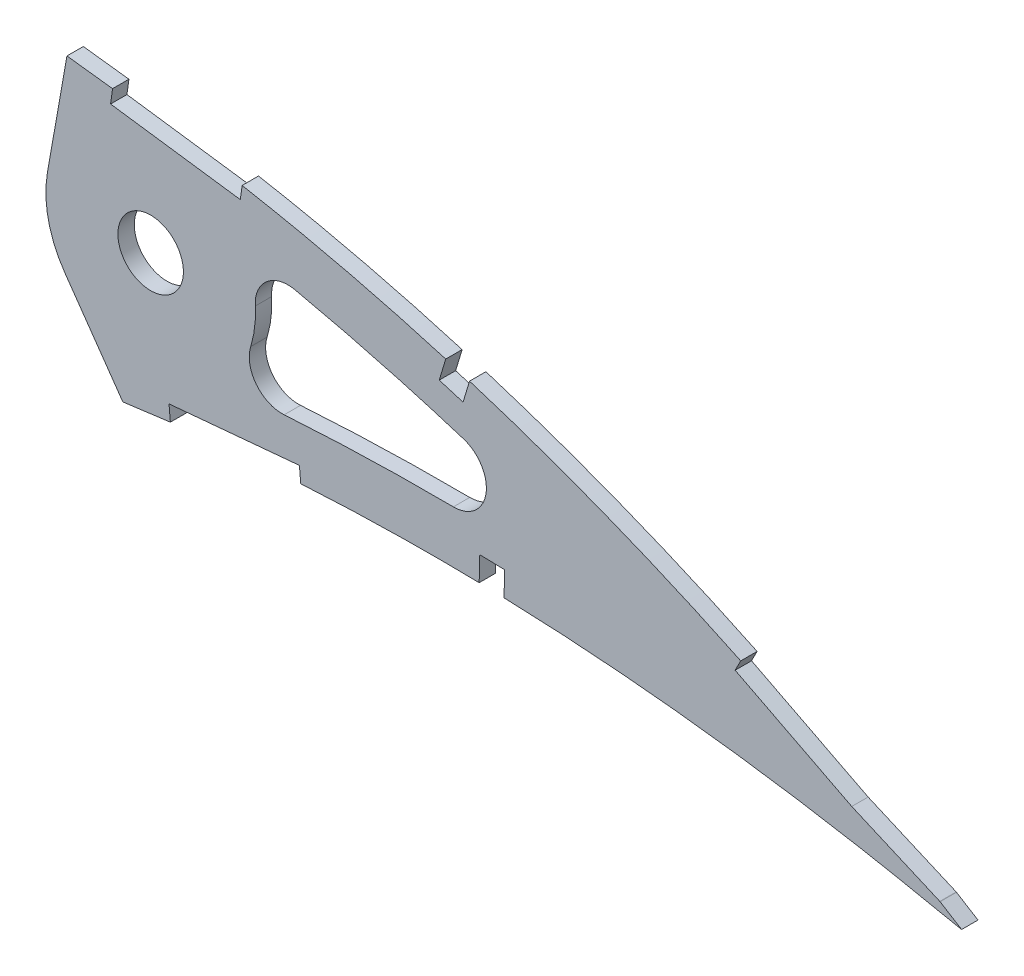
SolidWorks part; units mm, degrees
material "Pine"
ref_plane "Front Plane" through (0, 0, 0) normal (0, 0, 1) x (1, 0, 0)
ref_plane "Top Plane" through (0, 0, 0) normal (0, 1, 0) x (1, 0, 0)
ref_plane "Right Plane" through (0, 0, 0) normal (1, 0, 0) x (0, 0, -1)
curve "Curve2"
  spline degree 3 poles (520.229, 0.8111, 0) (520.1892, 0.8357, 0) (520.0299, 0.9341, 0) (519.6711, 1.1542, 0) (519.0735, 1.5208, 0) (518.237, 2.0313, 0) (517.1622, 2.6844, 0) (515.8486, 3.4756, 0) (514.2969, 4.4021, 0) (512.5075, 5.4598, 0) (510.4807, 6.6436, 0) (508.2172, 7.9486, 0) (505.7172, 9.3676, 0) (502.9816, 10.8948, 0) (500.0114, 12.5227, 0) (496.8072, 14.2443, 0) (493.3701, 16.0505, 0) (489.7015, 17.9338, 0) (485.8019, 19.8836, 0) (481.6733, 21.8919, 0) (477.317, 23.9487, 0) (472.7345, 26.0429, 0) (467.9284, 28.1661, 0) (462.9001, 30.305, 0) (457.6524, 32.4505, 0) (452.1876, 34.5902, 0) (446.5089, 36.7144, 0) (440.6184, 38.8094, 0) (434.5207, 40.866, 0) (428.2186, 42.8708, 0) (421.7166, 44.813, 0) (415.0186, 46.68, 0) (408.1302, 48.4622, 0) (401.0555, 50.1466, 0) (393.8008, 51.7219, 0) (386.3718, 53.1787, 0) (378.7746, 54.5024, 0) (371.0303, 55.692, 0) (363.2636, 56.6815, 0) (355.5128, 57.652, 0) (347.7736, 58.5637, 0) (339.9398, 59.4368, 0) (332.019, 60.2663, 0) (324.019, 61.0497, 0) (315.9478, 61.7836, 0) (307.814, 62.4658, 0) (299.6253, 63.0925, 0) (291.3904, 63.6628, 0) (283.1174, 64.1714, 0) (274.8152, 64.6183, 0) (266.4922, 65.0001, 0) (258.157, 65.3142, 0) (249.8185, 65.5589, 0) (241.4854, 65.7316, 0) (233.1666, 65.8314, 0) (224.8708, 65.8555, 0) (216.6071, 65.8035, 0) (208.384, 65.6736, 0) (200.2107, 65.464, 0) (192.0958, 65.1743, 0) (184.048, 64.8046, 0) (176.0762, 64.3519, 0) (168.189, 63.8191, 0) (160.3952, 63.2038, 0) (152.7034, 62.506, 0) (145.1216, 61.7286, 0) (137.6583, 60.8693, 0) (130.3214, 59.9308, 0) (123.1191, 58.9147, 0) (116.0593, 57.8206, 0) (109.1496, 56.6517, 0) (102.3976, 55.409, 0) (95.8102, 54.0963, 0) (89.3948, 52.714, 0) (83.1581, 51.266, 0) (77.1065, 49.7551, 0) (71.2467, 48.1838, 0) (65.5845, 46.5561, 0) (60.1256, 44.8756, 0) (54.8764, 43.1442, 0) (49.8409, 41.3683, 0) (45.0253, 39.5493, 0) (40.4333, 37.6928, 0) (36.0702, 35.8014, 0) (31.9393, 33.8806, 0) (28.0452, 31.9329, 0) (24.3908, 29.9636, 0) (20.9797, 27.9757, 0) (17.8153, 25.973, 0) (14.8987, 23.9604, 0) (12.2341, 21.9394, 0) (9.8224, 19.9149, 0) (7.6651, 17.8901, 0) (5.7652, 15.8664, 0) (4.1228, 13.8473, 0) (2.7399, 11.8344, 0) (1.6168, 9.8297, 0) (0.7561, 7.8345, 0) (0.1568, 5.85, 0) (-0.1712, 3.8792, 0) (-0.2528, 1.9205, 0) (-0.0842, 0.6392, 0) (0, 0, 0) knots 0 0 0 0 0.000254 0.001015 0.002283 0.004057 0.006331 0.009105 0.012374 0.016134 0.02038 0.025106 0.030306 0.035972 0.0421 0.048678 0.055702 0.06316 0.071046 0.07935 0.088063 0.097176 0.106678 0.116562 0.126814 0.137428 0.148394 0.1597 0.171338 0.183298 0.19557 0.208144 0.221012 0.234162 0.247587 0.261277 0.275223 0.289414 0.303771 0.317689 0.331784 0.34604 0.360444 0.374983 0.38964 0.404403 0.419257 0.434187 0.449177 0.464215 0.479284 0.49437 0.509458 0.524532 0.539579 0.554583 0.56953 0.584403 0.599191 0.613877 0.628447 0.642889 0.657186 0.671326 0.685294 0.699078 0.712665 0.726043 0.739198 0.752118 0.764792 0.777208 0.789356 0.801224 0.812804 0.824083 0.835055 0.84571 0.856038 0.866034 0.875689 0.884998 0.893953 0.902553 0.910789 0.918661 0.926166 0.933303 0.940071 0.946475 0.952518 0.958205 0.963547 0.968557 0.97325 0.977651 0.981787 0.985694 0.989415 0.993001 0.996508 1 1 1 1
curve "Curve3"
  spline degree 3 poles (0, 0, 0) (0.1336, -0.6306, 0) (0.4014, -1.8948, 0) (1.129, -3.7148, 0) (2.0912, -5.4642, 0) (3.3081, -7.1386, 0) (4.7718, -8.7374, 0) (6.479, -10.2623, 0) (8.428, -11.7125, 0) (10.6162, -13.0874, 0) (13.0406, -14.3883, 0) (15.6982, -15.6145, 0) (18.5868, -16.7656, 0) (21.7032, -17.8401, 0) (25.0435, -18.8396, 0) (28.6046, -19.7616, 0) (32.3825, -20.6074, 0) (36.3735, -21.375, 0) (40.5732, -22.065, 0) (44.9774, -22.6771, 0) (49.5814, -23.2117, 0) (54.3808, -23.6676, 0) (59.3708, -24.0458, 0) (64.5464, -24.3466, 0) (69.9027, -24.5709, 0) (75.4344, -24.718, 0) (81.1363, -24.7899, 0) (87.003, -24.788, 0) (93.0289, -24.7115, 0) (99.2088, -24.5648, 0) (105.5368, -24.3469, 0) (112.0073, -24.0604, 0) (118.6142, -23.7083, 0) (125.3518, -23.2917, 0) (132.2141, -22.8125, 0) (139.1951, -22.2745, 0) (146.2885, -21.679, 0) (153.4882, -21.0296, 0) (160.7876, -20.3295, 0) (168.1806, -19.5808, 0) (175.6606, -18.7872, 0) (183.2209, -17.9512, 0) (190.8551, -17.0772, 0) (198.5563, -16.1668, 0) (206.3179, -15.2253, 0) (214.1326, -14.2544, 0) (221.9939, -13.2579, 0) (229.8947, -12.2404, 0) (237.8276, -11.2019, 0) (245.786, -10.1497, 0) (253.7621, -9.0829, 0) (261.7491, -8.0072, 0) (269.7395, -6.9257, 0) (277.7256, -5.8389, 0) (285.7003, -4.7513, 0) (293.6562, -3.6657, 0) (301.5856, -2.5824, 0) (309.4812, -1.5067, 0) (317.3352, -0.4385, 0) (325.1402, 0.6201, 0) (332.8888, 1.6659, 0) (340.5737, 2.6975, 0) (348.187, 3.7144, 0) (355.721, 4.7168, 0) (363.0553, 5.6745, 0) (370.1707, 6.6383, 0) (377.0913, 7.4284, 0) (383.9258, 8.1028, 0) (390.6811, 8.6557, 0) (397.3493, 9.0951, 0) (403.9227, 9.4241, 0) (410.3934, 9.6473, 0) (416.7532, 9.7713, 0) (422.9943, 9.7993, 0) (429.1081, 9.7402, 0) (435.0867, 9.5987, 0) (440.9216, 9.3813, 0) (446.6049, 9.0952, 0) (452.1283, 8.7483, 0) (457.4837, 8.3456, 0) (462.6634, 7.8966, 0) (467.6597, 7.4078, 0) (472.4647, 6.8849, 0) (477.0715, 6.3387, 0) (481.4727, 5.7729, 0) (485.6616, 5.1968, 0) (489.6316, 4.6162, 0) (493.3764, 4.0385, 0) (496.89, 3.4693, 0) (500.1667, 2.916, 0) (503.2016, 2.384, 0) (505.9892, 1.8782, 0) (508.5257, 1.4052, 0) (510.8062, 0.9673, 0) (512.8275, 0.5717, 0) (514.5859, 0.2202, 0) (516.0789, -0.0824, 0) (517.3037, -0.3347, 0) (518.2586, -0.5328, 0) (518.9417, -0.6767, 0) (519.3522, -0.7624, 0) (519.5346, -0.8013, 0) (519.5802, -0.8111, 0) knots 0 0 0 0 0.003638 0.007293 0.011028 0.014901 0.018963 0.023258 0.027821 0.032679 0.037853 0.043362 0.049215 0.055422 0.061989 0.068918 0.076211 0.083868 0.091887 0.100266 0.109 0.118085 0.127515 0.137285 0.147388 0.157816 0.168563 0.179619 0.190977 0.202627 0.21456 0.226767 0.239236 0.251959 0.264924 0.27812 0.291536 0.30516 0.318981 0.332985 0.347163 0.361499 0.375981 0.390597 0.405333 0.420175 0.43511 0.450124 0.465203 0.480333 0.495501 0.51069 0.525887 0.541078 0.556247 0.571382 0.586466 0.601485 0.616424 0.631269 0.646007 0.660621 0.675098 0.689423 0.703582 0.716908 0.730009 0.742952 0.755726 0.76832 0.780724 0.792927 0.804916 0.816679 0.828204 0.839475 0.850481 0.861208 0.871639 0.881763 0.891564 0.901027 0.910139 0.918884 0.927249 0.935221 0.942785 0.949928 0.956638 0.962904 0.968712 0.974054 0.978918 0.983297 0.98718 0.990561 0.993433 0.995791 0.99763 0.998946 0.999737 1 1 1 1
sketch "Sketch1" plane through (0, 0, 0) normal (0, 0, 1) x (1, 0, 0)
  line L1 (519.5802, -0.8111) -> (524.4049, -1.7687)
  line L2 (520.229, 0.8111) -> (524.4049, -1.7687)
  spline S0 degree 3 poles (-2903.7635, -749.124) (66.2436, 68.8235) (-8.6937, 20.855) (1.129, -3.7148) (2.0912, -5.4642) (3.3081, -7.1386) (4.7718, -8.7374) (6.479, -10.2623) (8.428, -11.7125) (10.6162, -13.0874) (13.0406, -14.3883) (15.6982, -15.6145) (18.5868, -16.7656) (21.7032, -17.8401) (25.0435, -18.8396) (28.6046, -19.7616) (32.3825, -20.6074) (36.3735, -21.375) (40.5732, -22.065) (44.9774, -22.6771) (49.5814, -23.2117) (54.3808, -23.6676) (59.3708, -24.0458) (64.5464, -24.3466) (69.9027, -24.5709) (75.4344, -24.718) (81.1363, -24.7899) (87.003, -24.788) (93.0289, -24.7115) (99.2088, -24.5648) (105.5368, -24.3469) (112.0073, -24.0604) (118.6142, -23.7083) (125.3518, -23.2917) (132.2141, -22.8125) (139.1951, -22.2745) (146.2885, -21.679) (153.4882, -21.0296) (160.7876, -20.3295) (168.1806, -19.5808) (175.6606, -18.7872) (183.2209, -17.9512) (190.8551, -17.0772) (198.5563, -16.1668) (206.3179, -15.2253) (214.1326, -14.2544) (221.9939, -13.2579) (229.8947, -12.2404) (237.8276, -11.2019) (245.786, -10.1497) (253.7621, -9.0829) (261.7491, -8.0072) (269.7395, -6.9257) (277.7256, -5.8389) (285.7003, -4.7513) (293.6562, -3.6657) (301.5856, -2.5824) (309.4812, -1.5067) (317.3352, -0.4385) (325.1402, 0.6201) (332.8888, 1.6659) (340.5737, 2.6975) (348.187, 3.7144) (355.721, 4.7168) (363.0553, 5.6745) (370.1707, 6.6383) (377.0913, 7.4284) (383.9258, 8.1028) (390.6811, 8.6557) (397.3493, 9.0951) (403.9227, 9.4241) (410.3934, 9.6473) (416.7532, 9.7713) (422.9943, 9.7993) (429.1081, 9.7402) (435.0867, 9.5987) (440.9216, 9.3813) (446.6049, 9.0952) (452.1283, 8.7483) (457.4837, 8.3456) (462.6634, 7.8966) (467.6597, 7.4078) (472.4647, 6.8849) (477.0715, 6.3387) (481.4727, 5.7729) (485.6616, 5.1968) (489.6316, 4.6162) (493.3764, 4.0385) (496.89, 3.4693) (500.1667, 2.916) (503.2016, 2.384) (505.9892, 1.8782) (508.5257, 1.4052) (510.8062, 0.9673) (512.8275, 0.5717) (514.5859, 0.2202) (516.0789, -0.0824) (517.3037, -0.3347) (518.2586, -0.5328) (518.9417, -0.6767) (537.0698, -4.4604) (553.3394, -15.9066) (1193.1482, 2921.6684) knots -0.137857 -0.137857 -0.137857 -0.137857 0.003638 0.007293 0.011028 0.014901 0.018963 0.023258 0.027821 0.032679 0.037853 0.043362 0.049215 0.055422 0.061989 0.068918 0.076211 0.083868 0.091887 0.100266 0.109 0.118085 0.127515 0.137285 0.147388 0.157816 0.168563 0.179619 0.190977 0.202627 0.21456 0.226767 0.239236 0.251959 0.264924 0.27812 0.291536 0.30516 0.318981 0.332985 0.347163 0.361499 0.375981 0.390597 0.405333 0.420175 0.43511 0.450124 0.465203 0.480333 0.495501 0.51069 0.525887 0.541078 0.556247 0.571382 0.586466 0.601485 0.616424 0.631269 0.646007 0.660621 0.675098 0.689423 0.703582 0.716908 0.730009 0.742952 0.755726 0.76832 0.780724 0.792927 0.804916 0.816679 0.828204 0.839475 0.850481 0.861208 0.871639 0.881763 0.891564 0.901027 0.910139 0.918884 0.927249 0.935221 0.942785 0.949928 0.956638 0.962904 0.968712 0.974054 0.978918 0.983297 0.98718 0.990561 0.993433 0.995791 0.99763 0.998946 0.999737 1.102307 1.102307 1.102307 1.102307 only from (0, 0) to (519.5802, -0.8111) construction
  spline S1 degree 3 poles (2144.5607, 2521.6799) (550.9976, -26.3511) (537.2872, -9.6513) (519.6711, 1.1542) (519.0735, 1.5208) (518.237, 2.0313) (517.1622, 2.6844) (515.8486, 3.4756) (514.2969, 4.4021) (512.5075, 5.4598) (510.4807, 6.6436) (508.2172, 7.9486) (505.7172, 9.3676) (502.9816, 10.8948) (500.0114, 12.5227) (496.8072, 14.2443) (493.3701, 16.0505) (489.7015, 17.9338) (485.8019, 19.8836) (481.6733, 21.8919) (477.317, 23.9487) (472.7345, 26.0429) (467.9284, 28.1661) (462.9001, 30.305) (457.6524, 32.4505) (452.1876, 34.5902) (446.5089, 36.7144) (440.6184, 38.8094) (434.5207, 40.866) (428.2186, 42.8708) (421.7166, 44.813) (415.0186, 46.68) (408.1302, 48.4622) (401.0555, 50.1466) (393.8008, 51.7219) (386.3718, 53.1787) (378.7746, 54.5024) (371.0303, 55.692) (363.2636, 56.6815) (355.5128, 57.652) (347.7736, 58.5637) (339.9398, 59.4368) (332.019, 60.2663) (324.019, 61.0497) (315.9478, 61.7836) (307.814, 62.4658) (299.6253, 63.0925) (291.3904, 63.6628) (283.1174, 64.1714) (274.8152, 64.6183) (266.4922, 65.0001) (258.157, 65.3142) (249.8185, 65.5589) (241.4854, 65.7316) (233.1666, 65.8314) (224.8708, 65.8555) (216.6071, 65.8035) (208.384, 65.6736) (200.2107, 65.464) (192.0958, 65.1743) (184.048, 64.8046) (176.0762, 64.3519) (168.189, 63.8191) (160.3952, 63.2038) (152.7034, 62.506) (145.1216, 61.7286) (137.6583, 60.8693) (130.3214, 59.9308) (123.1191, 58.9147) (116.0593, 57.8206) (109.1496, 56.6517) (102.3976, 55.409) (95.8102, 54.0963) (89.3948, 52.714) (83.1581, 51.266) (77.1065, 49.7551) (71.2467, 48.1838) (65.5845, 46.5561) (60.1256, 44.8756) (54.8764, 43.1442) (49.8409, 41.3683) (45.0253, 39.5493) (40.4333, 37.6928) (36.0702, 35.8014) (31.9393, 33.8806) (28.0452, 31.9329) (24.3908, 29.9636) (20.9797, 27.9757) (17.8153, 25.973) (14.8987, 23.9604) (12.2341, 21.9394) (9.8224, 19.9149) (7.6651, 17.8901) (5.7652, 15.8664) (4.1228, 13.8473) (2.7399, 11.8344) (1.6168, 9.8297) (0.7561, 7.8345) (0.1568, 5.85) (-0.1712, 3.8792) (-1.2714, -22.5145) (85.5395, -42.7616) (-2987.8188, -259.5241) knots -0.109813 -0.109813 -0.109813 -0.109813 0.000254 0.001015 0.002283 0.004057 0.006331 0.009105 0.012374 0.016134 0.02038 0.025106 0.030306 0.035972 0.0421 0.048678 0.055702 0.06316 0.071046 0.07935 0.088063 0.097176 0.106678 0.116562 0.126814 0.137428 0.148394 0.1597 0.171338 0.183298 0.19557 0.208144 0.221012 0.234162 0.247587 0.261277 0.275223 0.289414 0.303771 0.317689 0.331784 0.34604 0.360444 0.374983 0.38964 0.404403 0.419257 0.434187 0.449177 0.464215 0.479284 0.49437 0.509458 0.524532 0.539579 0.554583 0.56953 0.584403 0.599191 0.613877 0.628447 0.642889 0.657186 0.671326 0.685294 0.699078 0.712665 0.726043 0.739198 0.752118 0.764792 0.777208 0.789356 0.801224 0.812804 0.824083 0.835055 0.84571 0.856038 0.866034 0.875689 0.884998 0.893953 0.902553 0.910789 0.918661 0.926166 0.933303 0.940071 0.946475 0.952518 0.958205 0.963547 0.968557 0.97325 0.977651 0.981787 0.985694 0.989415 0.993001 0.996508 1.132043 1.132043 1.132043 1.132043 only from (520.229, 0.8111) to (0, 0) construction
  spline S2 degree 3 poles (0, 0) (0.1336, -0.6306) (0.4014, -1.8948) (1.129, -3.7148) (2.0912, -5.4642) (3.3081, -7.1386) (4.7718, -8.7374) (6.479, -10.2623) (8.428, -11.7125) (10.6162, -13.0874) (13.0406, -14.3883) (15.6982, -15.6145) (18.5868, -16.7656) (21.7032, -17.8401) (25.0435, -18.8396) (28.6046, -19.7616) (32.3825, -20.6074) (36.3735, -21.375) (40.5732, -22.065) (44.9774, -22.6771) (49.5814, -23.2117) (54.3808, -23.6676) (59.3708, -24.0458) (64.5464, -24.3466) (69.9027, -24.5709) (75.4344, -24.718) (81.1363, -24.7899) (87.003, -24.788) (93.0289, -24.7115) (99.2088, -24.5648) (105.5368, -24.3469) (112.0073, -24.0604) (118.6142, -23.7083) (125.3518, -23.2917) (132.2141, -22.8125) (139.1951, -22.2745) (146.2885, -21.679) (153.4882, -21.0296) (160.7876, -20.3295) (168.1806, -19.5808) (175.6606, -18.7872) (183.2209, -17.9512) (190.8551, -17.0772) (198.5563, -16.1668) (206.3179, -15.2253) (214.1326, -14.2544) (221.9939, -13.2579) (229.8947, -12.2404) (237.8276, -11.2019) (245.786, -10.1497) (253.7621, -9.0829) (261.7491, -8.0072) (269.7395, -6.9257) (277.7256, -5.8389) (285.7003, -4.7513) (293.6562, -3.6657) (301.5856, -2.5824) (309.4812, -1.5067) (317.3352, -0.4385) (325.1402, 0.6201) (332.8888, 1.6659) (340.5737, 2.6975) (348.187, 3.7144) (355.721, 4.7168) (363.0553, 5.6745) (370.1707, 6.6383) (377.0913, 7.4284) (383.9258, 8.1028) (390.6811, 8.6557) (397.3493, 9.0951) (403.9227, 9.4241) (410.3934, 9.6473) (416.7532, 9.7713) (422.9943, 9.7993) (429.1081, 9.7402) (435.0867, 9.5987) (440.9216, 9.3813) (446.6049, 9.0952) (452.1283, 8.7483) (457.4837, 8.3456) (462.6634, 7.8966) (467.6597, 7.4078) (472.4647, 6.8849) (477.0715, 6.3387) (481.4727, 5.7729) (485.6616, 5.1968) (489.6316, 4.6162) (493.3764, 4.0385) (496.89, 3.4693) (500.1667, 2.916) (503.2016, 2.384) (505.9892, 1.8782) (508.5257, 1.4052) (510.8062, 0.9673) (512.8275, 0.5717) (514.5859, 0.2202) (516.0789, -0.0824) (517.3037, -0.3347) (518.2586, -0.5328) (518.9417, -0.6767) (519.3522, -0.7624) (519.5346, -0.8013) (519.5802, -0.8111) knots 0 0 0 0 0.003638 0.007293 0.011028 0.014901 0.018963 0.023258 0.027821 0.032679 0.037853 0.043362 0.049215 0.055422 0.061989 0.068918 0.076211 0.083868 0.091887 0.100266 0.109 0.118085 0.127515 0.137285 0.147388 0.157816 0.168563 0.179619 0.190977 0.202627 0.21456 0.226767 0.239236 0.251959 0.264924 0.27812 0.291536 0.30516 0.318981 0.332985 0.347163 0.361499 0.375981 0.390597 0.405333 0.420175 0.43511 0.450124 0.465203 0.480333 0.495501 0.51069 0.525887 0.541078 0.556247 0.571382 0.586466 0.601485 0.616424 0.631269 0.646007 0.660621 0.675098 0.689423 0.703582 0.716908 0.730009 0.742952 0.755726 0.76832 0.780724 0.792927 0.804916 0.816679 0.828204 0.839475 0.850481 0.861208 0.871639 0.881763 0.891564 0.901027 0.910139 0.918884 0.927249 0.935221 0.942785 0.949928 0.956638 0.962904 0.968712 0.974054 0.978918 0.983297 0.98718 0.990561 0.993433 0.995791 0.99763 0.998946 0.999737 1 1 1 1
  spline S3 degree 3 poles (520.229, 0.8111) (520.1892, 0.8357) (520.0299, 0.9341) (519.6711, 1.1542) (519.0735, 1.5208) (518.237, 2.0313) (517.1622, 2.6844) (515.8486, 3.4756) (514.2969, 4.4021) (512.5075, 5.4598) (510.4807, 6.6436) (508.2172, 7.9486) (505.7172, 9.3676) (502.9816, 10.8948) (500.0114, 12.5227) (496.8072, 14.2443) (493.3701, 16.0505) (489.7015, 17.9338) (485.8019, 19.8836) (481.6733, 21.8919) (477.317, 23.9487) (472.7345, 26.0429) (467.9284, 28.1661) (462.9001, 30.305) (457.6524, 32.4505) (452.1876, 34.5902) (446.5089, 36.7144) (440.6184, 38.8094) (434.5207, 40.866) (428.2186, 42.8708) (421.7166, 44.813) (415.0186, 46.68) (408.1302, 48.4622) (401.0555, 50.1466) (393.8008, 51.7219) (386.3718, 53.1787) (378.7746, 54.5024) (371.0303, 55.692) (363.2636, 56.6815) (355.5128, 57.652) (347.7736, 58.5637) (339.9398, 59.4368) (332.019, 60.2663) (324.019, 61.0497) (315.9478, 61.7836) (307.814, 62.4658) (299.6253, 63.0925) (291.3904, 63.6628) (283.1174, 64.1714) (274.8152, 64.6183) (266.4922, 65.0001) (258.157, 65.3142) (249.8185, 65.5589) (241.4854, 65.7316) (233.1666, 65.8314) (224.8708, 65.8555) (216.6071, 65.8035) (208.384, 65.6736) (200.2107, 65.464) (192.0958, 65.1743) (184.048, 64.8046) (176.0762, 64.3519) (168.189, 63.8191) (160.3952, 63.2038) (152.7034, 62.506) (145.1216, 61.7286) (137.6583, 60.8693) (130.3214, 59.9308) (123.1191, 58.9147) (116.0593, 57.8206) (109.1496, 56.6517) (102.3976, 55.409) (95.8102, 54.0963) (89.3948, 52.714) (83.1581, 51.266) (77.1065, 49.7551) (71.2467, 48.1838) (65.5845, 46.5561) (60.1256, 44.8756) (54.8764, 43.1442) (49.8409, 41.3683) (45.0253, 39.5493) (40.4333, 37.6928) (36.0702, 35.8014) (31.9393, 33.8806) (28.0452, 31.9329) (24.3908, 29.9636) (20.9797, 27.9757) (17.8153, 25.973) (14.8987, 23.9604) (12.2341, 21.9394) (9.8224, 19.9149) (7.6651, 17.8901) (5.7652, 15.8664) (4.1228, 13.8473) (2.7399, 11.8344) (1.6168, 9.8297) (0.7561, 7.8345) (0.1568, 5.85) (-0.1712, 3.8792) (-0.2528, 1.9205) (-0.0842, 0.6392) (0, 0) knots 0 0 0 0 0.000254 0.001015 0.002283 0.004057 0.006331 0.009105 0.012374 0.016134 0.02038 0.025106 0.030306 0.035972 0.0421 0.048678 0.055702 0.06316 0.071046 0.07935 0.088063 0.097176 0.106678 0.116562 0.126814 0.137428 0.148394 0.1597 0.171338 0.183298 0.19557 0.208144 0.221012 0.234162 0.247587 0.261277 0.275223 0.289414 0.303771 0.317689 0.331784 0.34604 0.360444 0.374983 0.38964 0.404403 0.419257 0.434187 0.449177 0.464215 0.479284 0.49437 0.509458 0.524532 0.539579 0.554583 0.56953 0.584403 0.599191 0.613877 0.628447 0.642889 0.657186 0.671326 0.685294 0.699078 0.712665 0.726043 0.739198 0.752118 0.764792 0.777208 0.789356 0.801224 0.812804 0.824083 0.835055 0.84571 0.856038 0.866034 0.875689 0.884998 0.893953 0.902553 0.910789 0.918661 0.926166 0.933303 0.940071 0.946475 0.952518 0.958205 0.963547 0.968557 0.97325 0.977651 0.981787 0.985694 0.989415 0.993001 0.996508 1 1 1 1
extrude "Boss-Extrude1" add sketch "Sketch1" along normal blind 3.175
sketch "Sketch4" plane through (0, 0, 0) normal (0, 0, -1) x (-1, 0, 0)
  line L0 (-347.1309, 36.7611) -> (-350.9097, 58.1919)
  line L1 (-350.497, 21.5775) -> (-361.7496, 5.5072)
  line L2 (-520.229, 0.8111) -> (-524.4049, -1.7687)
  line L3 (-524.4049, -1.7687) -> (-519.5802, -0.8111)
  line L6 (-367.1422, 33.2326) -> (-394.958, 33.2326)
  circle A0 centre (-367.1422, 33.2326) radius 20.32
  circle A1 centre (-367.1422, 33.2326) radius 6.35
  spline S0 degree 1 poles (-521.6997, 9.1254) (-10.022, 1.7185) knots 0 0 1 1 construction
  spline S1 degree 1 poles (-10.022, 1.7185) (-514.8893, -7.8326) knots 0 0 1 1 construction
  spline S2 degree 3 poles (2987.4901, -259.5009) (-85.5334, -42.7602) (1.2713, -22.5136) (0.1712, 3.8792) (-0.1568, 5.85) (-0.7561, 7.8345) (-1.6168, 9.8297) (-2.7399, 11.8344) (-4.1228, 13.8473) (-5.7652, 15.8664) (-7.6651, 17.8901) (-9.8224, 19.9149) (-12.2341, 21.9394) (-14.8987, 23.9604) (-17.8153, 25.973) (-20.9797, 27.9757) (-24.3908, 29.9636) (-28.0452, 31.9329) (-31.9393, 33.8806) (-36.0702, 35.8014) (-40.4333, 37.6928) (-45.0253, 39.5493) (-49.8409, 41.3683) (-54.8764, 43.1442) (-60.1256, 44.8756) (-65.5845, 46.5561) (-71.2467, 48.1838) (-77.1065, 49.7551) (-83.1581, 51.266) (-89.3948, 52.714) (-95.8102, 54.0963) (-102.3976, 55.409) (-109.1496, 56.6517) (-116.0593, 57.8206) (-123.1191, 58.9147) (-130.3214, 59.9308) (-137.6583, 60.8693) (-145.1216, 61.7286) (-152.7034, 62.506) (-160.3952, 63.2038) (-168.189, 63.8191) (-176.0762, 64.3519) (-184.048, 64.8046) (-192.0958, 65.1743) (-200.2107, 65.464) (-208.384, 65.6736) (-216.6071, 65.8035) (-224.8708, 65.8555) (-233.1666, 65.8314) (-241.4854, 65.7316) (-249.8185, 65.5589) (-258.157, 65.3142) (-266.4922, 65.0001) (-274.8152, 64.6183) (-283.1174, 64.1714) (-291.3904, 63.6628) (-299.6253, 63.0925) (-307.814, 62.4658) (-315.9478, 61.7836) (-324.019, 61.0497) (-332.019, 60.2663) (-339.9398, 59.4368) (-347.7736, 58.5637) (-355.5128, 57.652) (-363.2636, 56.6815) (-371.0303, 55.692) (-378.7746, 54.5024) (-386.3718, 53.1787) (-393.8008, 51.7219) (-401.0555, 50.1466) (-408.1302, 48.4622) (-415.0186, 46.68) (-421.7166, 44.813) (-428.2186, 42.8708) (-434.5207, 40.866) (-440.6184, 38.8094) (-446.5089, 36.7144) (-452.1876, 34.5902) (-457.6524, 32.4505) (-462.9001, 30.305) (-467.9284, 28.1661) (-472.7345, 26.0429) (-477.317, 23.9487) (-481.6733, 21.8919) (-485.8019, 19.8836) (-489.7015, 17.9338) (-493.3701, 16.0505) (-496.8072, 14.2443) (-500.0114, 12.5227) (-502.9816, 10.8948) (-505.7172, 9.3676) (-508.2172, 7.9486) (-510.4807, 6.6436) (-512.5075, 5.4598) (-514.2969, 4.4021) (-515.8486, 3.4756) (-517.1622, 2.6844) (-518.237, 2.0313) (-519.0735, 1.5208) (-519.6711, 1.1542) (-537.2876, -9.6516) (-550.9983, -26.352) (-2144.6851, 2521.8788) knots -0.132038 -0.132038 -0.132038 -0.132038 0.003492 0.006999 0.010585 0.014306 0.018213 0.022349 0.02675 0.031443 0.036453 0.041795 0.047482 0.053525 0.059929 0.066697 0.073834 0.081339 0.089211 0.097447 0.106047 0.115002 0.124311 0.133966 0.143962 0.15429 0.164945 0.175917 0.187196 0.198776 0.210644 0.222792 0.235208 0.247882 0.260802 0.273957 0.287335 0.300922 0.314706 0.328674 0.342814 0.357111 0.371553 0.386123 0.400809 0.415597 0.43047 0.445417 0.460421 0.475468 0.490542 0.50563 0.520716 0.535785 0.550823 0.565813 0.580743 0.595597 0.61036 0.625017 0.639556 0.65396 0.668216 0.682311 0.696229 0.710586 0.724777 0.738723 0.752413 0.765838 0.778988 0.791856 0.80443 0.816702 0.828662 0.8403 0.851606 0.862572 0.873186 0.883438 0.893322 0.902824 0.911937 0.92065 0.928954 0.93684 0.944298 0.951322 0.9579 0.964028 0.969694 0.974894 0.97962 0.983866 0.987626 0.990895 0.993669 0.995943 0.997717 0.998985 0.999746 1.109816 1.109816 1.109816 1.109816 only from (0, 0) to (-520.229, 0.8111)
  spline S3 degree 3 poles (-1193.1472, 2921.6638) (-553.3393, -15.9066) (-537.0698, -4.4604) (-518.9417, -0.6767) (-518.2586, -0.5328) (-517.3037, -0.3347) (-516.0789, -0.0824) (-514.5859, 0.2202) (-512.8275, 0.5717) (-510.8062, 0.9673) (-508.5257, 1.4052) (-505.9892, 1.8782) (-503.2016, 2.384) (-500.1667, 2.916) (-496.89, 3.4693) (-493.3764, 4.0385) (-489.6316, 4.6162) (-485.6616, 5.1968) (-481.4727, 5.7729) (-477.0715, 6.3387) (-472.4647, 6.8849) (-467.6597, 7.4078) (-462.6634, 7.8966) (-457.4837, 8.3456) (-452.1283, 8.7483) (-446.6049, 9.0952) (-440.9216, 9.3813) (-435.0867, 9.5987) (-429.1081, 9.7402) (-422.9943, 9.7993) (-416.7532, 9.7713) (-410.3934, 9.6473) (-403.9227, 9.4241) (-397.3493, 9.0951) (-390.6811, 8.6557) (-383.9258, 8.1028) (-377.0913, 7.4284) (-370.1707, 6.6383) (-363.0553, 5.6745) (-355.721, 4.7168) (-348.187, 3.7144) (-340.5737, 2.6975) (-332.8888, 1.6659) (-325.1402, 0.6201) (-317.3352, -0.4385) (-309.4812, -1.5067) (-301.5856, -2.5824) (-293.6562, -3.6657) (-285.7003, -4.7513) (-277.7256, -5.8389) (-269.7395, -6.9257) (-261.7491, -8.0072) (-253.7621, -9.0829) (-245.786, -10.1497) (-237.8276, -11.2019) (-229.8947, -12.2404) (-221.9939, -13.2579) (-214.1326, -14.2544) (-206.3179, -15.2253) (-198.5563, -16.1668) (-190.8551, -17.0772) (-183.2209, -17.9512) (-175.6606, -18.7872) (-168.1806, -19.5808) (-160.7876, -20.3295) (-153.4882, -21.0296) (-146.2885, -21.679) (-139.1951, -22.2745) (-132.2141, -22.8125) (-125.3518, -23.2917) (-118.6142, -23.7083) (-112.0073, -24.0604) (-105.5368, -24.3469) (-99.2088, -24.5648) (-93.0289, -24.7115) (-87.003, -24.788) (-81.1363, -24.7899) (-75.4344, -24.718) (-69.9027, -24.5709) (-64.5464, -24.3466) (-59.3708, -24.0458) (-54.3808, -23.6676) (-49.5814, -23.2117) (-44.9774, -22.6771) (-40.5732, -22.065) (-36.3735, -21.375) (-32.3825, -20.6074) (-28.6046, -19.7616) (-25.0435, -18.8396) (-21.7032, -17.8401) (-18.5868, -16.7656) (-15.6982, -15.6145) (-13.0406, -14.3883) (-10.6162, -13.0874) (-8.428, -11.7125) (-6.479, -10.2623) (-4.7718, -8.7374) (-3.3081, -7.1386) (-2.0912, -5.4642) (-1.129, -3.7148) (8.6936, 20.8547) (-66.2416, 68.8223) (2903.6435, -749.0909) knots -0.102307 -0.102307 -0.102307 -0.102307 0.000263 0.001054 0.00237 0.004209 0.006567 0.009439 0.01282 0.016703 0.021082 0.025946 0.031288 0.037096 0.043362 0.050072 0.057215 0.064779 0.072751 0.081116 0.089861 0.098973 0.108436 0.118237 0.128361 0.138792 0.149519 0.160525 0.171796 0.183321 0.195084 0.207073 0.219276 0.23168 0.244274 0.257048 0.269991 0.283092 0.296418 0.310577 0.324902 0.339379 0.353993 0.368731 0.383576 0.398515 0.413534 0.428618 0.443753 0.458922 0.474113 0.48931 0.504499 0.519667 0.534797 0.549876 0.56489 0.579825 0.594667 0.609403 0.624019 0.638501 0.652837 0.667015 0.681019 0.69484 0.708464 0.72188 0.735076 0.748041 0.760764 0.773233 0.78544 0.797373 0.809023 0.820381 0.831437 0.842184 0.852612 0.862715 0.872485 0.881915 0.891 0.899734 0.908113 0.916132 0.923789 0.931082 0.938011 0.944578 0.950785 0.956638 0.962147 0.967321 0.972179 0.976742 0.981037 0.985099 0.988972 0.992707 0.996362 1.137855 1.137855 1.137855 1.137855 only from (-519.5802, -0.8111) to (0, 0)
  spline S4 degree 3 poles (0, 0) (0.0842, 0.6392) (0.2528, 1.9205) (0.1712, 3.8792) (-0.1568, 5.85) (-0.7561, 7.8345) (-1.6168, 9.8297) (-2.7399, 11.8344) (-4.1228, 13.8473) (-5.7652, 15.8664) (-7.6651, 17.8901) (-9.8224, 19.9149) (-12.2341, 21.9394) (-14.8987, 23.9604) (-17.8153, 25.973) (-20.9797, 27.9757) (-24.3908, 29.9636) (-28.0452, 31.9329) (-31.9393, 33.8806) (-36.0702, 35.8014) (-40.4333, 37.6928) (-45.0253, 39.5493) (-49.8409, 41.3683) (-54.8764, 43.1442) (-60.1256, 44.8756) (-65.5845, 46.5561) (-71.2467, 48.1838) (-77.1065, 49.7551) (-83.1581, 51.266) (-89.3948, 52.714) (-95.8102, 54.0963) (-102.3976, 55.409) (-109.1496, 56.6517) (-116.0593, 57.8206) (-123.1191, 58.9147) (-130.3214, 59.9308) (-137.6583, 60.8693) (-145.1216, 61.7286) (-152.7034, 62.506) (-160.3952, 63.2038) (-168.189, 63.8191) (-176.0762, 64.3519) (-184.048, 64.8046) (-192.0958, 65.1743) (-200.2107, 65.464) (-208.384, 65.6736) (-216.6071, 65.8035) (-224.8708, 65.8555) (-233.1666, 65.8314) (-241.4854, 65.7316) (-249.8185, 65.5589) (-258.157, 65.3142) (-266.4922, 65.0001) (-274.8152, 64.6183) (-283.1174, 64.1714) (-291.3904, 63.6628) (-299.6253, 63.0925) (-307.814, 62.4658) (-315.9478, 61.7836) (-324.019, 61.0497) (-332.019, 60.2663) (-339.9398, 59.4368) (-347.7736, 58.5637) (-355.5128, 57.652) (-363.2636, 56.6815) (-371.0303, 55.692) (-378.7746, 54.5024) (-386.3718, 53.1787) (-393.8008, 51.7219) (-401.0555, 50.1466) (-408.1302, 48.4622) (-415.0186, 46.68) (-421.7166, 44.813) (-428.2186, 42.8708) (-434.5207, 40.866) (-440.6184, 38.8094) (-446.5089, 36.7144) (-452.1876, 34.5902) (-457.6524, 32.4505) (-462.9001, 30.305) (-467.9284, 28.1661) (-472.7345, 26.0429) (-477.317, 23.9487) (-481.6733, 21.8919) (-485.8019, 19.8836) (-489.7015, 17.9338) (-493.3701, 16.0505) (-496.8072, 14.2443) (-500.0114, 12.5227) (-502.9816, 10.8948) (-505.7172, 9.3676) (-508.2172, 7.9486) (-510.4807, 6.6436) (-512.5075, 5.4598) (-514.2969, 4.4021) (-515.8486, 3.4756) (-517.1622, 2.6844) (-518.237, 2.0313) (-519.0735, 1.5208) (-519.6711, 1.1542) (-520.0299, 0.9341) (-520.1892, 0.8357) (-520.229, 0.8111) knots 0 0 0 0 0.003492 0.006999 0.010585 0.014306 0.018213 0.022349 0.02675 0.031443 0.036453 0.041795 0.047482 0.053525 0.059929 0.066697 0.073834 0.081339 0.089211 0.097447 0.106047 0.115002 0.124311 0.133966 0.143962 0.15429 0.164945 0.175917 0.187196 0.198776 0.210644 0.222792 0.235208 0.247882 0.260802 0.273957 0.287335 0.300922 0.314706 0.328674 0.342814 0.357111 0.371553 0.386123 0.400809 0.415597 0.43047 0.445417 0.460421 0.475468 0.490542 0.50563 0.520716 0.535785 0.550823 0.565813 0.580743 0.595597 0.61036 0.625017 0.639556 0.65396 0.668216 0.682311 0.696229 0.710586 0.724777 0.738723 0.752413 0.765838 0.778988 0.791856 0.80443 0.816702 0.828662 0.8403 0.851606 0.862572 0.873186 0.883438 0.893322 0.902824 0.911937 0.92065 0.928954 0.93684 0.944298 0.951322 0.9579 0.964028 0.969694 0.974894 0.97962 0.983866 0.987626 0.990895 0.993669 0.995943 0.997717 0.998985 0.999746 1 1 1 1
  spline S5 degree 3 poles (-519.5802, -0.8111) (-519.5346, -0.8013) (-519.3522, -0.7624) (-518.9417, -0.6767) (-518.2586, -0.5328) (-517.3037, -0.3347) (-516.0789, -0.0824) (-514.5859, 0.2202) (-512.8275, 0.5717) (-510.8062, 0.9673) (-508.5257, 1.4052) (-505.9892, 1.8782) (-503.2016, 2.384) (-500.1667, 2.916) (-496.89, 3.4693) (-493.3764, 4.0385) (-489.6316, 4.6162) (-485.6616, 5.1968) (-481.4727, 5.7729) (-477.0715, 6.3387) (-472.4647, 6.8849) (-467.6597, 7.4078) (-462.6634, 7.8966) (-457.4837, 8.3456) (-452.1283, 8.7483) (-446.6049, 9.0952) (-440.9216, 9.3813) (-435.0867, 9.5987) (-429.1081, 9.7402) (-422.9943, 9.7993) (-416.7532, 9.7713) (-410.3934, 9.6473) (-403.9227, 9.4241) (-397.3493, 9.0951) (-390.6811, 8.6557) (-383.9258, 8.1028) (-377.0913, 7.4284) (-370.1707, 6.6383) (-363.0553, 5.6745) (-355.721, 4.7168) (-348.187, 3.7144) (-340.5737, 2.6975) (-332.8888, 1.6659) (-325.1402, 0.6201) (-317.3352, -0.4385) (-309.4812, -1.5067) (-301.5856, -2.5824) (-293.6562, -3.6657) (-285.7003, -4.7513) (-277.7256, -5.8389) (-269.7395, -6.9257) (-261.7491, -8.0072) (-253.7621, -9.0829) (-245.786, -10.1497) (-237.8276, -11.2019) (-229.8947, -12.2404) (-221.9939, -13.2579) (-214.1326, -14.2544) (-206.3179, -15.2253) (-198.5563, -16.1668) (-190.8551, -17.0772) (-183.2209, -17.9512) (-175.6606, -18.7872) (-168.1806, -19.5808) (-160.7876, -20.3295) (-153.4882, -21.0296) (-146.2885, -21.679) (-139.1951, -22.2745) (-132.2141, -22.8125) (-125.3518, -23.2917) (-118.6142, -23.7083) (-112.0073, -24.0604) (-105.5368, -24.3469) (-99.2088, -24.5648) (-93.0289, -24.7115) (-87.003, -24.788) (-81.1363, -24.7899) (-75.4344, -24.718) (-69.9027, -24.5709) (-64.5464, -24.3466) (-59.3708, -24.0458) (-54.3808, -23.6676) (-49.5814, -23.2117) (-44.9774, -22.6771) (-40.5732, -22.065) (-36.3735, -21.375) (-32.3825, -20.6074) (-28.6046, -19.7616) (-25.0435, -18.8396) (-21.7032, -17.8401) (-18.5868, -16.7656) (-15.6982, -15.6145) (-13.0406, -14.3883) (-10.6162, -13.0874) (-8.428, -11.7125) (-6.479, -10.2623) (-4.7718, -8.7374) (-3.3081, -7.1386) (-2.0912, -5.4642) (-1.129, -3.7148) (-0.4014, -1.8948) (-0.1336, -0.6306) (0, 0) knots 0 0 0 0 0.000263 0.001054 0.00237 0.004209 0.006567 0.009439 0.01282 0.016703 0.021082 0.025946 0.031288 0.037096 0.043362 0.050072 0.057215 0.064779 0.072751 0.081116 0.089861 0.098973 0.108436 0.118237 0.128361 0.138792 0.149519 0.160525 0.171796 0.183321 0.195084 0.207073 0.219276 0.23168 0.244274 0.257048 0.269991 0.283092 0.296418 0.310577 0.324902 0.339379 0.353993 0.368731 0.383576 0.398515 0.413534 0.428618 0.443753 0.458922 0.474113 0.48931 0.504499 0.519667 0.534797 0.549876 0.56489 0.579825 0.594667 0.609403 0.624019 0.638501 0.652837 0.667015 0.681019 0.69484 0.708464 0.72188 0.735076 0.748041 0.760764 0.773233 0.78544 0.797373 0.809023 0.820381 0.831437 0.842184 0.852612 0.862715 0.872485 0.881915 0.891 0.899734 0.908113 0.916132 0.923789 0.931082 0.938011 0.944578 0.950785 0.956638 0.962147 0.967321 0.972179 0.976742 0.981037 0.985099 0.988972 0.992707 0.996362 1 1 1 1
  spline S6 degree 3 poles (-521.6997, 9.1254) (-521.5185, 9.1641) (-521.1414, 9.2431) (-520.5013, 9.3777) (-519.6014, 9.5652) (-518.5867, 9.7745) (-516.5017, 10.2002) (-512.0338, 11.0895) (-502.3328, 12.9034) (-482.8666, 16.0553) (-454.7955, 19.1487) (-426.5367, 20.1772) (-403.9091, 19.6864) (-389.7949, 18.8264) (-379.9243, 17.9283) (-374.3105, 17.3355) (-370.0824, 16.8486) (-365.8505, 16.3062) (-361.7465, 15.7537) (-357.6653, 15.2168) (-352.1695, 14.4949) (-345.3171, 13.5814) (-334.359, 12.1168) (-315.179, 9.5288) (-287.8082, 5.789) (-254.9835, 1.3131) (-222.1895, -3.0348) (-189.4106, -7.0959) (-156.654, -10.6508) (-129.3813, -12.9449) (-107.6083, -14.1485) (-91.3205, -14.6521) (-75.1074, -14.6475) (-61.7108, -14.0897) (-51.1341, -13.1896) (-43.3067, -12.2396) (-35.6411, -10.9589) (-28.237, -9.2636) (-21.2892, -7.0583) (-16.2032, -4.6866) (-13.0461, -2.5478) (-11.6056, -1.201) (-10.836, -0.2227) (-10.5202, 0.2936) (-10.2886, 0.7695) (-10.2055, 0.9824) (-10.1785, 1.0643) (-10.1577, 1.1349) (-10.1105, 1.3225) (-10.0643, 1.5249) (-10.0354, 1.6565) (-10.022, 1.7185) knots 0 0 0 0 0.000976 0.001952 0.003903 0.005855 0.007806 0.015612 0.031224 0.062448 0.124896 0.187344 0.218569 0.249793 0.265405 0.273211 0.281017 0.288823 0.296629 0.304435 0.312241 0.327853 0.343465 0.374689 0.437137 0.499585 0.562033 0.624482 0.68693 0.749378 0.780602 0.811826 0.84305 0.874274 0.889886 0.905498 0.92111 0.936722 0.952334 0.967946 0.975753 0.983559 0.987462 0.991365 0.993316 0.995268 0.996243 0.997219 0.998195 0.998683 0.999171 0.999171 0.999171 0.999171
  spline S7 degree 3 poles (-10.022, 1.7185) (-10.0137, 1.7838) (-9.9964, 1.9227) (-9.9722, 2.1338) (-9.9548, 2.3267) (-9.9521, 2.385) (-9.9503, 2.4853) (-9.9613, 2.7344) (-10.0122, 3.1442) (-10.0839, 3.5102) (-10.2224, 4.0331) (-10.6171, 5.1175) (-11.6184, 6.9252) (-14.1026, 10.0907) (-18.4256, 14.0534) (-24.6526, 18.4028) (-31.4923, 22.3392) (-38.7272, 25.9013) (-46.2345, 29.1355) (-56.5074, 33.06) (-69.7207, 37.3231) (-85.9449, 41.5978) (-102.4194, 45.1568) (-124.6274, 49.0726) (-152.7038, 52.5874) (-186.6719, 55.0054) (-220.784, 55.8886) (-254.9542, 55.4386) (-289.1234, 53.7977) (-317.5664, 51.5306) (-337.4323, 49.5018) (-348.7883, 48.2227) (-357.2614, 47.1962) (-365.8396, 46.1279) (-374.0765, 44.9754) (-382.3862, 43.5815) (-393.3717, 41.4855) (-407.0282, 38.3742) (-428.6204, 32.3912) (-455.0706, 23.0586) (-480.6155, 11.4116) (-497.9507, 2.1395) (-506.4753, -2.765) (-510.6983, -5.2786) (-512.8069, -6.557) (-513.8432, -7.1901) (-514.4641, -7.5709) (-514.7453, -7.7437) (-514.8893, -7.8326) knots 0.000796 0.000796 0.000796 0.000796 0.001284 0.001772 0.002748 0.003724 0.004699 0.006651 0.008603 0.010554 0.012506 0.016409 0.024215 0.032021 0.047634 0.063247 0.078859 0.094472 0.110084 0.125697 0.156922 0.188147 0.219372 0.250597 0.313047 0.375498 0.437948 0.500398 0.562848 0.625299 0.656524 0.672136 0.687749 0.703361 0.718974 0.734587 0.750199 0.781424 0.812649 0.8751 0.93755 0.968775 0.984387 0.992194 0.996097 0.998048 0.999024 1 1 1 1
  dimension "D3" = 40.64
  dimension "D4" = 80
  dimension "D5" = 55
  dimension "D1" = 0
  dimension "D2" = 10.16
extrude "Cut-Extrude3" cut sketch "Sketch4" against normal through all
sketch "Sketch5" plane through (0, 0, 3.175) normal (0, 0, 1) x (1, 0, 0)
  line L1 (384.9613, 54.0165) -> (359.8038, 57.4907)
  line L3 (395.9844, 11.9659) -> (370.6988, 9.6537)
  line L5 (429.1179, 43.0703) -> (424.4993, 44.4641)
  line L7 (435.787, 14.3413) -> (430.9639, 14.4592)
  line L9 (504.4525, 11.1152) -> (481.935, 22.6423)
  line L11 (527.6665, 1.0588) -> (504.4525, 11.1152)
  line L13 (526.4044, -1.8545) -> (527.6665, 1.0588)
  line L15 (435.6691, 9.5183) -> (435.787, 14.3413)
  line L17 (396.2734, 8.8052) -> (395.9844, 11.9659)
  line L19 (427.7241, 38.4518) -> (429.1179, 43.0703)
  line L21 (384.527, 50.8718) -> (384.9613, 54.0165)
  line L23 (359.3695, 54.346) -> (384.527, 50.8718)
  line L25 (370.9878, 6.493) -> (396.2734, 8.8052)
  line L27 (423.1056, 39.8456) -> (427.7241, 38.4518)
  line L29 (430.8461, 9.6361) -> (435.6691, 9.5183)
  line L31 (480.4883, 19.8161) -> (503.0975, 8.2421)
  line L33 (503.0975, 8.2421) -> (526.4044, -1.8545)
  line L35 (424.4993, 44.4641) -> (423.1056, 39.8456)
  line L37 (359.8038, 57.4907) -> (359.3695, 54.346)
  line L39 (481.935, 22.6423) -> (480.4883, 19.8161)
  line L41 (430.9639, 14.4592) -> (430.8461, 9.6361)
  line L43 (370.6988, 9.6537) -> (370.9878, 6.493)
extrude "Cut-Extrude4" cut sketch "Sketch5" against normal blind 7.62
fillet "Fillet1" radius 6.35 3 edges at (466.3825, 17.7386, 1.5875) (380.5614, 17.9739, 1.5875) (384.9122, 43.088, 1.5875)
